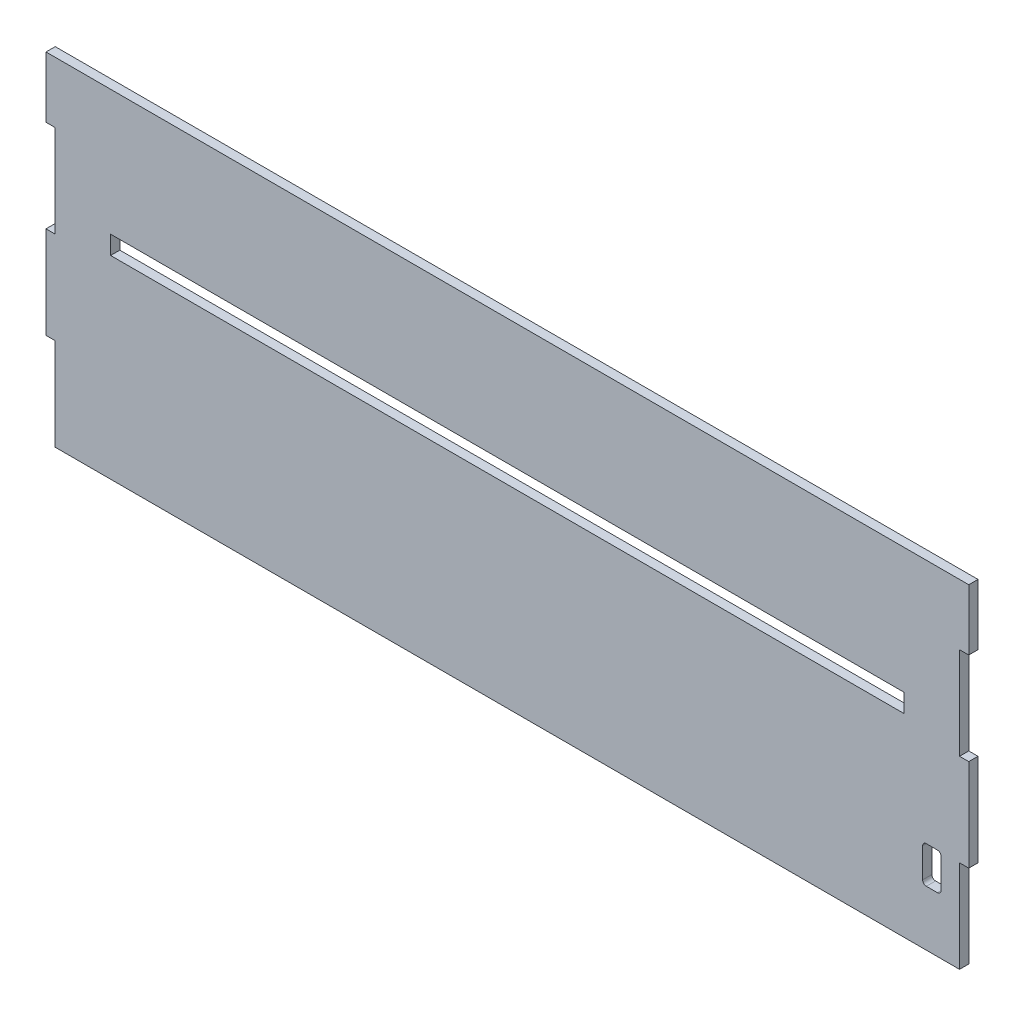
SolidWorks part; units mm, degrees
material "Contreplaqué pin"
ref_plane "Plan de face" through (0, 0, 0) normal (0, 0, 1) x (1, 0, 0)
ref_plane "Plan de dessus" through (0, 0, 0) normal (0, 1, 0) x (1, 0, 0)
ref_plane "Plan de droite" through (0, 0, 0) normal (1, 0, 0) x (0, 0, -1)
sketch "Esquisse1" plane through (0, 0, 0) normal (0, 0, 1) x (1, 0, 0)
  line L0 (0, 50) -> (5, 50)
  line L1 (5, 0) -> (495, 0)
  line L2 (0, 50) -> (0, 100)
  line L3 (0, 183) -> (500, 183)
  line L4 (500, 50) -> (500, 100)
  line L5 (5, 50) -> (5, 0)
  line L6 (0, 100) -> (5, 100)
  line L7 (5, 100) -> (5, 150)
  line L8 (5, 150) -> (0, 150)
  line L9 (0, 150) -> (0, 183)
  line L10 (495, 0) -> (495, 50)
  line L11 (495, 50) -> (500, 50)
  line L12 (500, 100) -> (495, 100)
  line L13 (495, 100) -> (495, 150)
  line L14 (495, 150) -> (500, 150)
  line L15 (500, 150) -> (500, 183)
  line L16 (35, 110) -> (5, 110) construction
  line L17 (35, 115) -> (465, 115)
  line L18 (35, 115) -> (35, 105)
  line L19 (35, 105) -> (465, 105)
  line L20 (465, 115) -> (465, 105)
  line L21 (465, 110) -> (495, 110) construction
  dimension "D1" = 500
  dimension "D2" = 183
  dimension "D3" = 50
  dimension "D4" = 5
  dimension "D5" = 5
  dimension "D6" = 430
  dimension "D7" = 10
  dimension "D8" = 110
extrude "Boss.-Extru.1" add sketch "Esquisse1" along normal blind 5
sketch "Esquisse2" plane through (0, 0, 0) normal (0, 0, -1) x (-1, 0, 0)
  line L0 (-495, 0) -> (-495, 50) construction
  line L1 (-483, 30) -> (-477, 30)
  line L2 (-485, 32) -> (-485, 48)
  line L3 (-483, 50) -> (-477, 50)
  line L4 (-475, 32) -> (-475, 48)
  line L5 (-5, 0) -> (-495, 0) construction
  arc A0 (-475, 48) -> (-477, 50) centre (-477, 48) ccw
  arc A1 (-477, 30) -> (-475, 32) centre (-477, 32) ccw
  arc A2 (-485, 32) -> (-483, 30) centre (-483, 32) ccw
  arc A3 (-485, 48) -> (-483, 50) centre (-483, 48) cw
  dimension "D5" = 2
  dimension "D1" = 20
  dimension "D2" = 10
  dimension "D3" = 10
  dimension "D4" = 30
extrude "Enlèv. mat.-Extru.1" cut sketch "Esquisse2" against normal up to next
